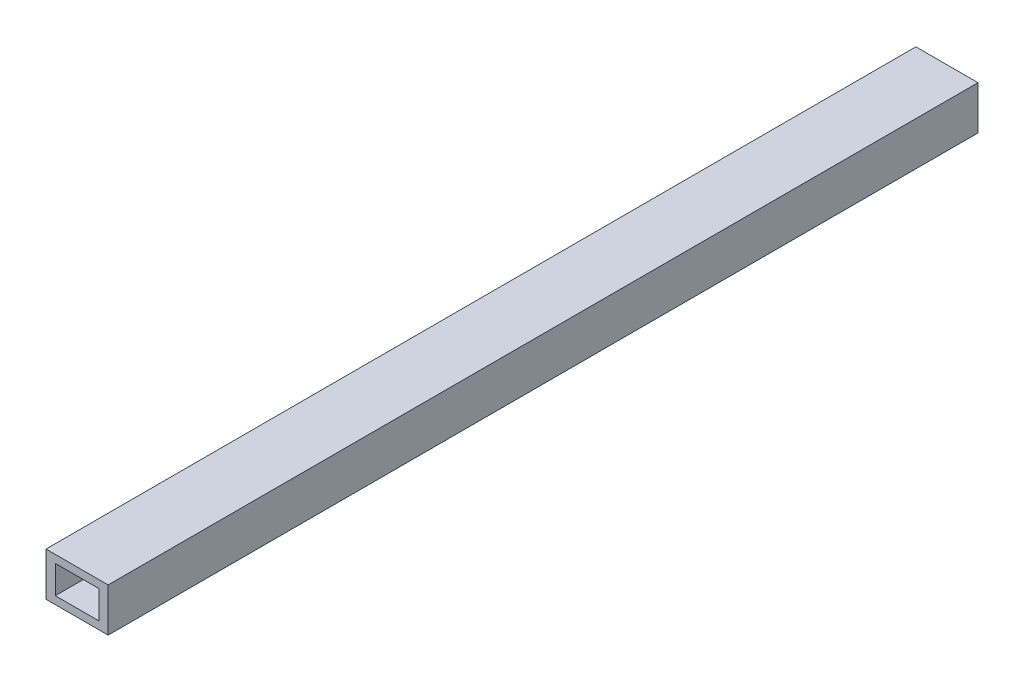
SolidWorks part; units mm, degrees
ref_plane "Front Plane" through (0, 0, 0) normal (0, 0, 1) x (1, 0, 0)
ref_plane "Top Plane" through (0, 0, 0) normal (0, 1, 0) x (1, 0, 0)
ref_plane "Right Plane" through (0, 0, 0) normal (1, 0, 0) x (0, 0, -1)
sketch "Sketch1" plane through (0, 0, 0) normal (0, 0, 1) x (1, 0, 0)
  line L1 (3.5, -2.2524) -> (-3.5, -2.2524)
  line L2 (3.5, -2.2524) -> (3.5, 2.2524)
  line L3 (3.5, 2.2524) -> (-3.5, 2.2524)
  line L4 (-3.5, -2.2524) -> (-3.5, 2.2524)
  line L7 (5, -3.5024) -> (-5, -3.5024)
  line L8 (5, -3.5024) -> (5, 3.5024)
  line L9 (5, 3.5024) -> (-5, 3.5024)
  line L10 (-5, -3.5024) -> (-5, 3.5024)
  point P0 (0, 0)
  point P6 (0, 0)
  dimension "D1" = 10
  dimension "D2" = 7.0048
  dimension "D3" = 1.5
  dimension "D4" = 1.25
extrude "Boss-Extrude1" add sketch "Sketch1" against normal blind 140
